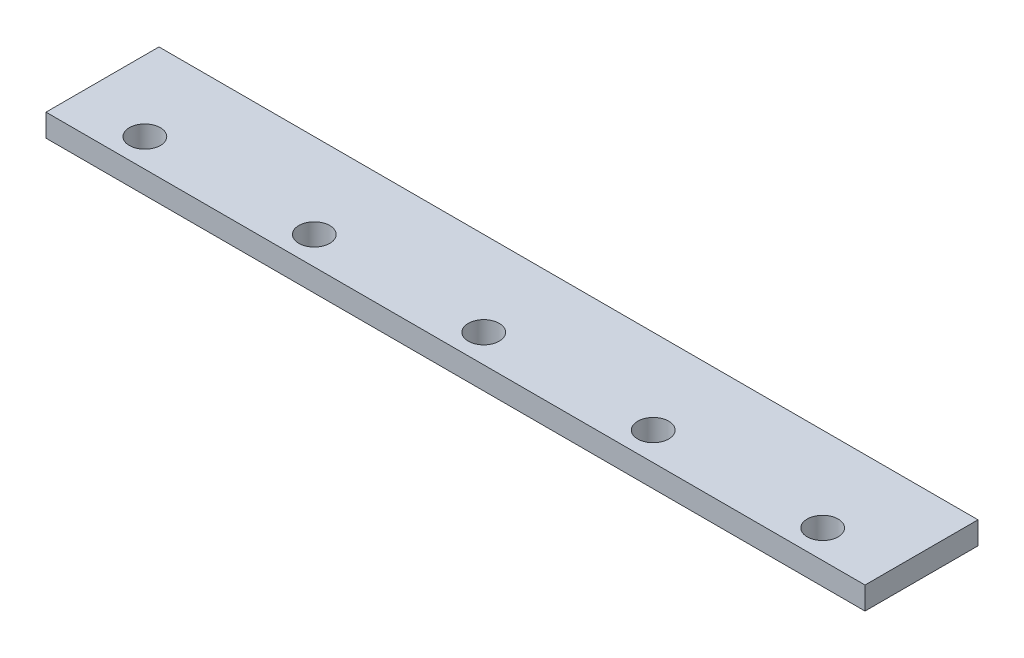
SolidWorks part; units mm, degrees
ref_plane "Front Plane" through (0, 0, 0) normal (0, 0, 1) x (1, 0, 0)
ref_plane "Top Plane" through (0, 0, 0) normal (0, 1, 0) x (1, 0, 0)
ref_plane "Right Plane" through (0, 0, 0) normal (1, 0, 0) x (0, 0, -1)
sketch "Sketch1" plane through (0, 0, 0) normal (0, 1, 0) x (1, 0, 0)
  line L1 (20.3152, -688.0911) -> (5820.3152, -688.0911)
  line L2 (20.3152, -688.0911) -> (20.3152, -1488.0911)
  line L3 (20.3152, -1488.0911) -> (5820.3152, -1488.0911)
  line L4 (5820.3152, -688.0911) -> (5820.3152, -1488.0911)
  dimension "D1" = 5800
  dimension "D2" = 800
extrude "Boss-Extrude1" add sketch "Sketch1" along normal blind 160
sketch "Sketch2" plane through (0, 160, 0) normal (0, 1, 0) x (1, 0, 0)
  line L0 (20.3152, -688.0911) -> (20.3152, -1488.0911) construction
  line L3 (20.3152, -1488.0911) -> (5820.3152, -1488.0911) construction
  circle A0 centre (520.3152, -1288.0911) radius 109.7053
  point P2 (0, 0)
  dimension "D1" = 500
  dimension "D2" = 200
extrude "Cut-Extrude1" cut sketch "Sketch2" against normal blind 160
pattern_linear "LPattern1" count 5 spacing 1200 along (1, 0, 0) of "Cut-Extrude1"
